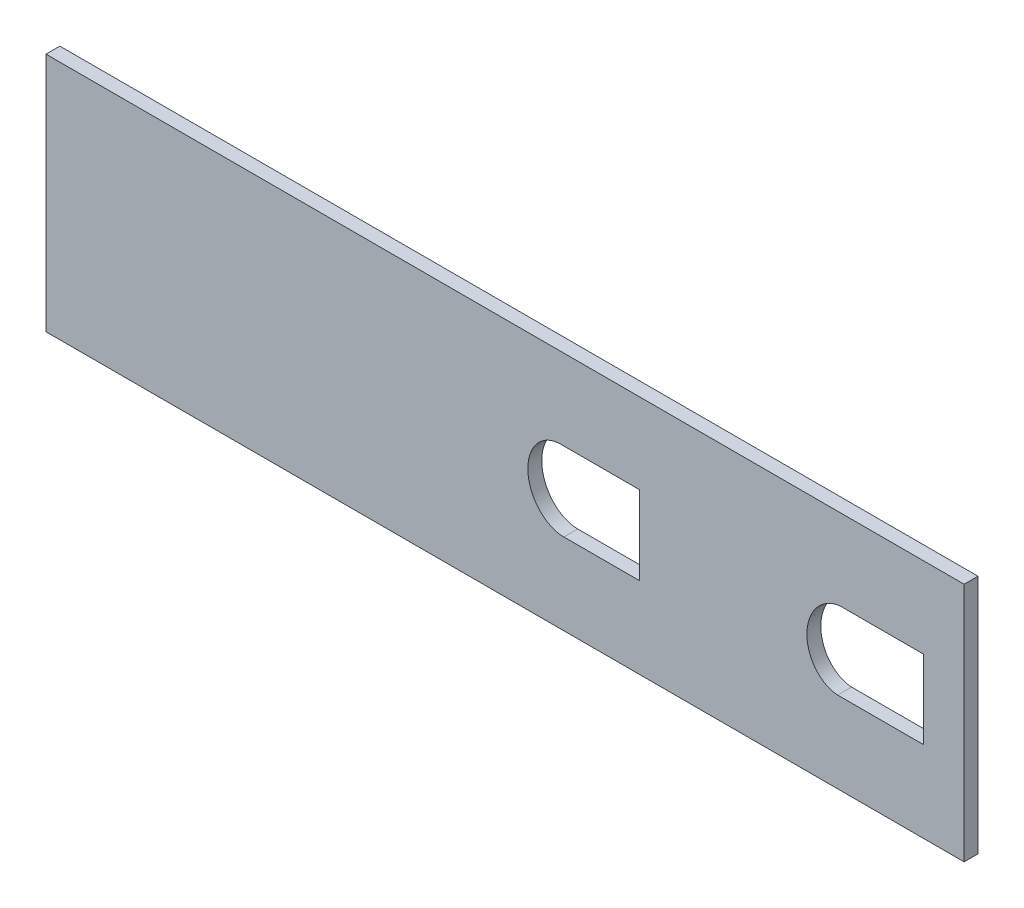
SolidWorks part; units mm, degrees
material "FiberBoard"
ref_plane "Front Plane" through (0, 0, 0) normal (0, 0, 1) x (1, 0, 0)
ref_plane "Top Plane" through (0, 0, 0) normal (0, 1, 0) x (1, 0, 0)
ref_plane "Right Plane" through (0, 0, 0) normal (1, 0, 0) x (0, 0, -1)
sketch "Sketch1" plane through (0, 0, 0) normal (0, 0, 1) x (1, 0, 0)
  line L1 (-366.5883, -417.497) -> (-366.5883, 16.4038) construction
  line L3 (-366.5883, 9.0583) -> (-156.5883, 9.0583)
  line L4 (-366.5883, 9.0583) -> (-366.5883, -45.9417)
  line L5 (-366.5883, -45.9417) -> (-156.5883, -45.9417)
  line L6 (-156.5883, 9.0583) -> (-156.5883, -45.9417)
  line L7 (-360.2383, -18.4417) -> (-176.7942, -18.4417) construction
  line L8 (-176.7942, -18.4417) -> (-156.5883, -18.4417) construction
  line L9 (-183.826, -9.4376) -> (-165.8259, -9.4376)
  line L10 (-165.8259, -9.4376) -> (-165.8259, -27.3597)
  line L11 (-165.8259, -27.3597) -> (-185.4981, -27.3597)
  line L12 (-248.8426, -9.3453) -> (-230.8426, -9.3453)
  line L13 (-230.8426, -9.3453) -> (-230.8426, -27.3596)
  line L14 (-230.8426, -27.3596) -> (-248.122, -27.3596)
  spline S2 degree 3 poles (-248.8426, -9.3453) (-249.0085, -9.3453) (-249.1745, -9.3512) (-249.8979, -9.4031) (-250.439, -9.5088) (-251.2269, -9.7643) (-251.4869, -9.8664) (-251.9919, -10.1009) (-252.4785, -10.3637) (-252.9306, -10.6798) (-253.3659, -11.0219) (-253.5762, -11.2071) (-254.1706, -11.7902) (-254.5211, -12.2164) (-254.984, -12.9071) (-255.1282, -13.1469) (-255.391, -13.6351) (-255.5103, -13.8842) (-255.8333, -14.6456) (-256.0031, -15.1742) (-256.2501, -16.2584) (-256.3256, -16.8046) (-256.3719, -17.6295) (-256.3762, -17.9055) (-256.3624, -18.4592) (-256.3442, -18.738) (-256.2576, -19.5642) (-256.1573, -20.1052) (-255.9427, -20.9018) (-255.8605, -21.1649) (-255.6739, -21.6858) (-255.5689, -21.9448) (-255.225, -22.7015) (-254.9569, -23.181) (-254.496, -23.8626) (-254.3325, -24.0834) (-253.9849, -24.5118) (-253.7999, -24.7204) (-253.2179, -25.3179) (-252.7997, -25.6744) (-252.1253, -26.144) (-251.8926, -26.2896) (-251.4102, -26.5573) (-251.1589, -26.6802) (-250.3898, -27.0046) (-249.863, -27.161) (-249.051, -27.3027) (-248.7767, -27.3343) (-248.3732, -27.3562) (-248.2475, -27.3596) (-248.122, -27.3596) knots 0.990687 0.990687 0.990687 0.990687 1 1 1.03125 1.03125 1.046875 1.046875 1.0625 1.078125 1.078125 1.09375 1.09375 1.125 1.125 1.140625 1.140625 1.15625 1.15625 1.1875 1.1875 1.21875 1.21875 1.234375 1.234375 1.25 1.25 1.28125 1.28125 1.296875 1.296875 1.3125 1.3125 1.34375 1.34375 1.359375 1.359375 1.375 1.375 1.40625 1.40625 1.421875 1.421875 1.4375 1.4375 1.46875 1.46875 1.484375 1.484375 1.491412 1.491412 1.491412 1.491412
  spline S3 degree 3 poles (-183.826, -9.4376) (-184.3816, -9.3977) (-184.9305, -9.4248) (-186.0155, -9.607) (-186.5547, -9.7649) (-187.3162, -10.0827) (-187.5638, -10.2023) (-188.047, -10.4679) (-188.2836, -10.6147) (-188.9672, -11.0881) (-189.3858, -11.4452) (-190.1559, -12.2341) (-190.5079, -12.6685) (-191.1243, -13.5796) (-191.3923, -14.0595) (-191.7352, -14.8147) (-191.8397, -15.0728) (-192.0257, -15.5922) (-192.1077, -15.8546) (-192.3216, -16.6492) (-192.4218, -17.189) (-192.5083, -18.014) (-192.5264, -18.2916) (-192.5403, -18.8424) (-192.5363, -19.1168) (-192.4908, -19.9367) (-192.4164, -20.4791) (-192.2341, -21.286) (-192.1609, -21.5552) (-191.9925, -22.0811) (-191.8972, -22.3386) (-191.5782, -23.0947) (-191.3215, -23.577) (-190.8641, -24.2648) (-190.6983, -24.4895) (-190.347, -24.9172) (-190.1619, -25.1203) (-189.5777, -25.697) (-189.1503, -26.0384) (-188.445, -26.4777) (-188.199, -26.6116) (-187.6998, -26.8456) (-187.1899, -27.0484) (-186.6583, -27.1886) (-186.1156, -27.2967) (-185.8376, -27.3344) (-185.5406, -27.3568) (-185.5194, -27.3583) (-185.4981, -27.3597) knots 0 0 0 0 0.03125 0.03125 0.0625 0.0625 0.078125 0.078125 0.09375 0.09375 0.125 0.125 0.15625 0.15625 0.1875 0.1875 0.203125 0.203125 0.21875 0.21875 0.25 0.25 0.265625 0.265625 0.28125 0.28125 0.3125 0.3125 0.328125 0.328125 0.34375 0.34375 0.375 0.375 0.390625 0.390625 0.40625 0.40625 0.4375 0.4375 0.453125 0.453125 0.46875 0.484375 0.484375 0.5 0.5 0.501205 0.501205 0.501205 0.501205
  point P2 (-340.8969, 43.7495)
  point P10 (-156.5883, -18.4417)
  dimension "D1" = 210
  dimension "D2" = 55
  dimension "D3" = 18.0001
  dimension "D4" = 18
extrude "Boss-Extrude1" add sketch "Sketch1" along normal blind 3.175
